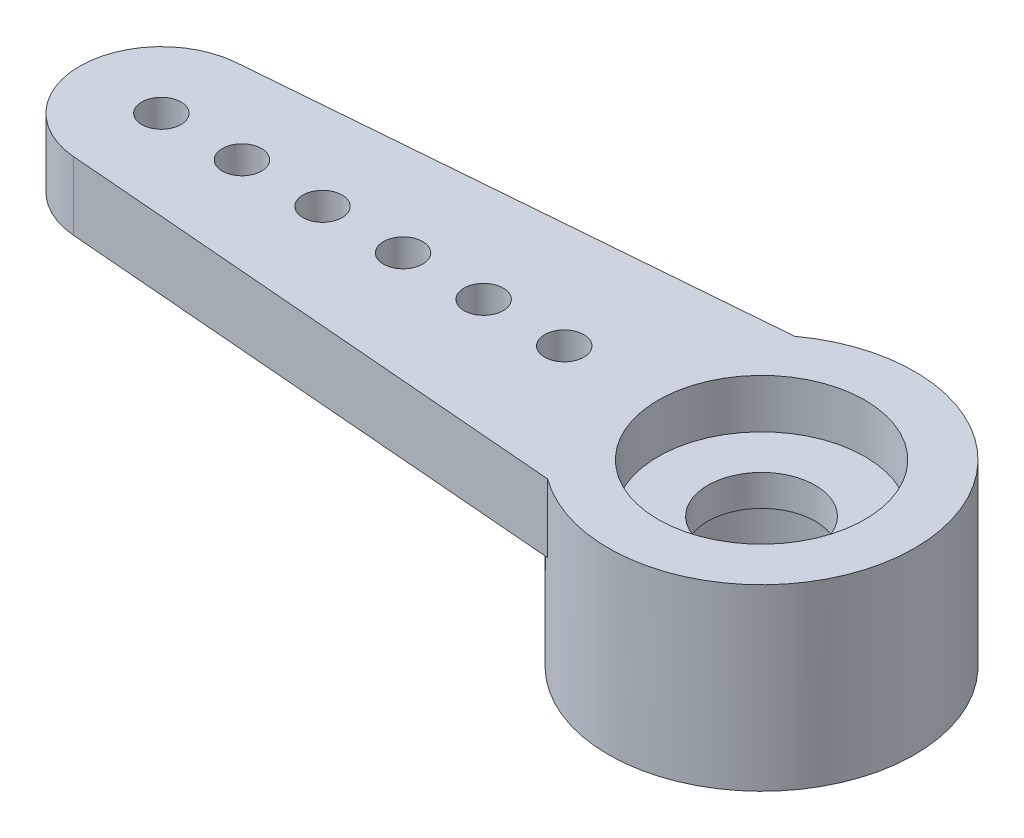
SolidWorks part; units mm, degrees
material "Nylon 101"
ref_plane "Front Plane" through (0, 0, 0) normal (0, 0, 1) x (1, 0, 0)
ref_plane "Top Plane" through (0, 0, 0) normal (0, 1, 0) x (1, 0, 0)
ref_plane "Right Plane" through (0, 0, 0) normal (1, 0, 0) x (0, 0, -1)
sketch "Sketch18" plane through (0, 0, 0) normal (0, 1, 0) x (1, 0, 0)
  line L0 (-16.1205, 0) -> (3.6195, 0) construction
  line L1 (-14.3472, 1.924) -> (-2.1374, 2.921)
  line L2 (-14.3472, -1.924) -> (-2.1374, -2.921)
  arc A0 (-2.1374, -2.921) -> (-2.1374, 2.921) centre (0, 0) ccw
  arc A1 (-14.3472, 1.924) -> (-14.3472, -1.924) centre (-14.1901, 0) ccw
  dimension "D1" = 1.9304
  dimension "D2" = 3.6195
  dimension "D3" = 19.74
  dimension "D4" = 5.842
extrude "Extrude17" add sketch "Sketch18" along normal blind 1.6129
sketch "Sketch19" plane through (0, 1.6129, 0) normal (0, 1, 0) x (1, 0, 0)
  circle A0 centre (0, 0) radius 3.6195
  arc A1 (-2.1374, -2.921) -> (-2.1374, 2.921) centre (0, 0) ccw construction
extrude "Extrude19" add sketch "Sketch19" against normal blind 4.2291
sketch "Sketch20" plane through (0, 1.6129, 0) normal (0, 1, 0) x (1, 0, 0)
  line L0 (-14.1901, 0) -> (-12.2851, 0) construction
  line L1 (-12.2851, 0) -> (-10.3801, 0) construction
  line L2 (-10.3801, 0) -> (-8.4751, 0) construction
  line L3 (-8.4751, 0) -> (-6.5701, 0) construction
  line L4 (-6.5701, 0) -> (-4.6651, 0) construction
  line L5 (-4.6651, 0) -> (-2.7601, 0) construction
  line L6 (-2.7601, 0) -> (0, 0) construction
  circle A0 centre (-14.1901, 0) radius 0.4636
  circle A1 centre (0, 0) radius 1.27
  circle A3 centre (-4.6651, 0) radius 0.4636
  circle A4 centre (-6.5701, 0) radius 0.4636
  circle A5 centre (-8.4751, 0) radius 0.4636
  circle A6 centre (-10.3801, 0) radius 0.4636
  circle A7 centre (-12.2851, 0) radius 0.4636
  dimension "D1" = 0.9271
  dimension "D3" = 2.54
  dimension "D2" = 1.905
extrude "Extrude20" cut sketch "Sketch20" against normal through all
sketch "Sketch21" plane through (0, 1.6129, 0) normal (0, 1, 0) x (1, 0, 0)
  circle A0 centre (0, 0) radius 2.4447
  dimension "D1" = 4.8895
extrude "Extrude21" cut sketch "Sketch21" against normal blind 1.1557
sketch "Sketch22" plane through (0, -2.6162, 0) normal (0, -1, 0) x (1, 0, 0)
  circle A0 centre (0, 0) radius 2.286
  dimension "D1" = 4.572
extrude "Extrude22" cut sketch "Sketch22" against normal blind 2.3368
